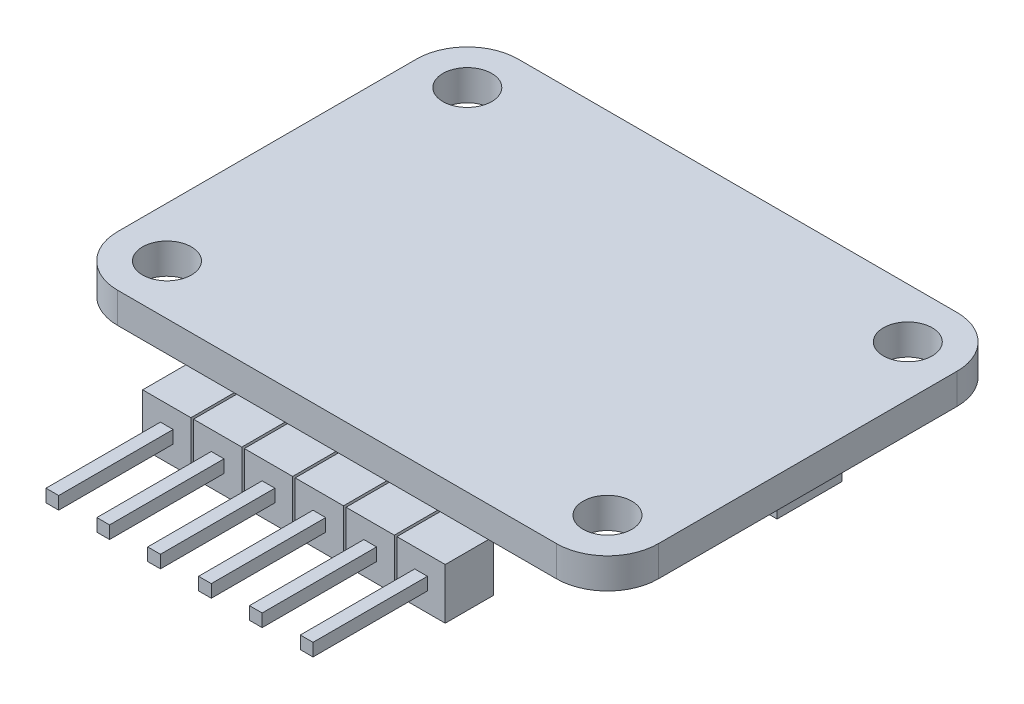
SolidWorks part; units mm, degrees
ref_plane "Front Plane" through (0, 0, 0) normal (0, 0, 1) x (1, 0, 0)
ref_plane "Top Plane" through (0, 0, 0) normal (0, 1, 0) x (1, 0, 0)
ref_plane "Right Plane" through (0, 0, 0) normal (1, 0, 0) x (0, 0, -1)
sketch "Sketch1" plane through (0, 0, 0) normal (0, 1, 0) x (1, 0, 0)
  line L0 (13.5, 20) -> (13.5, 0) construction
  line L1 (0, 20) -> (27, 20)
  line L2 (0, 20) -> (0, 0)
  line L3 (0, 0) -> (27, 0)
  line L4 (27, 20) -> (27, 0)
  line L5 (2.5, 10) -> (24.5, 10) construction
  line L6 (2.5, 17.5) -> (2.5, 2.5) construction
  line L7 (24.5, 17.5) -> (24.5, 2.5) construction
  circle A0 centre (2.5, 17.5) radius 1.2192
  circle A1 centre (24.5, 17.5) radius 1.2192
  circle A2 centre (24.5, 2.5) radius 1.2192
  circle A3 centre (2.5, 2.5) radius 1.2192
  point P13 (13.5, 10)
  dimension "D5" = 2.4384
  dimension "D1" = 27
  dimension "D2" = 20
  dimension "D3" = 22
  dimension "D4" = 15
extrude "Boss-Extrude1" add sketch "Sketch1" along normal blind 1.524
sketch "Sketch2" plane through (0, 1.524, 0) normal (0, 1, 0) x (1, 0, 0)
  line L0 (13.5, 1.524) -> (13.5, 0) construction
  line L1 (7.15, 1.524) -> (9.69, 1.524) construction
  line L2 (9.69, 1.524) -> (12.23, 1.524) construction
  line L3 (12.23, 1.524) -> (14.77, 1.524) construction
  line L4 (14.77, 1.524) -> (17.31, 1.524) construction
  line L5 (17.31, 1.524) -> (19.85, 1.524) construction
  line L6 (0, 0) -> (27, 0) construction
  line L7 (19.85, 1.524) -> (22.39, 1.524) construction
  line L8 (21.12, 12.54) -> (21.12, 7.46) construction
  line L9 (21.12, 10) -> (27, 10) construction
  line L10 (27, 0) -> (27, 20) construction
  line L11 (21.12, 7.46) -> (21.12, 1.524) construction
  point P10 (22.39, 10)
  dimension "D1" = 2.54
  dimension "D2" = 1.524
  dimension "D3" = 5.08
  dimension "D4" = 1.27
sketch "Sketch3" plane through (0, 0, 0) normal (0, -1, 0) x (-1, 0, 0)
  line L0 (-18.6435, -0.9525) -> (-18.5165, -0.9525) construction
  line L21 (-21.0565, 0.254) -> (-18.6435, 0.254)
  line L24 (-13.5635, -0.9525) -> (-13.4365, -0.9525) construction
  line L25 (-15.9765, 0.254) -> (-13.5635, 0.254)
  line L26 (-15.9765, 0.254) -> (-15.9765, -2.159)
  line L27 (-15.9765, -2.159) -> (-13.5635, -2.159)
  line L28 (-13.5635, 0.254) -> (-13.5635, -2.159)
  line L29 (-13.4365, 0.254) -> (-11.0235, 0.254)
  line L30 (-13.4365, 0.254) -> (-13.4365, -2.159)
  line L31 (-13.4365, -2.159) -> (-11.0235, -2.159)
  line L32 (-11.0235, 0.254) -> (-11.0235, -2.159)
  line L33 (-10.8965, 0.254) -> (-8.4835, 0.254)
  line L34 (-10.8965, 0.254) -> (-10.8965, -2.159)
  line L35 (-10.8965, -2.159) -> (-8.4835, -2.159)
  line L36 (-8.4835, 0.254) -> (-8.4835, -2.159)
  line L37 (-8.3565, 0.254) -> (-5.9435, 0.254)
  line L38 (-8.3565, 0.254) -> (-8.3565, -2.159)
  line L39 (-8.3565, -2.159) -> (-5.9435, -2.159)
  line L40 (-5.9435, 0.254) -> (-5.9435, -2.159)
  line L41 (-10.8965, -0.9525) -> (-11.0235, -0.9525) construction
  line L42 (-8.3565, -0.9525) -> (-8.4835, -0.9525) construction
  line L43 (-13.5, 1.524) -> (-13.5, 0) construction
  line L44 (0, 0) -> (-27, 0) construction
  line L45 (-21.0565, 0.254) -> (-21.0565, -2.159)
  line L46 (-21.0565, -2.159) -> (-18.6435, -2.159)
  line L47 (-18.6435, 0.254) -> (-18.6435, -2.159)
  line L48 (-18.5165, 0.254) -> (-16.1035, 0.254)
  line L49 (-18.5165, 0.254) -> (-18.5165, -2.159)
  line L50 (-18.5165, -2.159) -> (-16.1035, -2.159)
  line L51 (-16.1035, 0.254) -> (-16.1035, -2.159)
  line L53 (-15.9765, -0.9525) -> (-16.1035, -0.9525) construction
  point P27 (-13.5, -0.9525)
  dimension "D2" = 0.127
  dimension "D3" = 2.413
  dimension "D5" = 0.254
extrude "Boss-Extrude2" add sketch "Sketch3" along normal blind 2.54
sketch "Sketch4" plane through (0, 0, 2.159) normal (0, 0, 1) x (1, 0, 0)
  line L0 (8.3565, -1.27) -> (5.9435, -1.27) construction
  line L1 (5.9435, -2.54) -> (5.9435, 0) construction
  line L2 (8.3565, -2.54) -> (8.3565, 0) construction
  line L3 (17.6275, -0.9525) -> (16.9925, -0.9525)
  line L4 (17.6275, -0.9525) -> (17.6275, -1.5875)
  line L5 (7.15, -0.9525) -> (7.15, -1.5875) construction
  line L7 (7.4675, -0.9525) -> (7.4675, -1.5875)
  line L8 (7.4675, -0.9525) -> (6.8325, -0.9525)
  line L9 (6.8325, -0.9525) -> (6.8325, -1.5875)
  line L10 (7.4675, -1.5875) -> (6.8325, -1.5875)
  line L134 (10.0075, -0.9525) -> (9.3725, -0.9525)
  line L135 (10.0075, -0.9525) -> (10.0075, -1.5875)
  line L136 (10.0075, -1.5875) -> (9.3725, -1.5875)
  line L137 (9.3725, -0.9525) -> (9.3725, -1.5875)
  line L138 (12.5475, -0.9525) -> (11.9125, -0.9525)
  line L139 (12.5475, -0.9525) -> (12.5475, -1.5875)
  line L140 (12.5475, -1.5875) -> (11.9125, -1.5875)
  line L141 (11.9125, -0.9525) -> (11.9125, -1.5875)
  line L142 (15.0875, -0.9525) -> (14.4525, -0.9525)
  line L143 (15.0875, -0.9525) -> (15.0875, -1.5875)
  line L144 (15.0875, -1.5875) -> (14.4525, -1.5875)
  line L145 (14.4525, -0.9525) -> (14.4525, -1.5875)
  line L146 (17.6275, -1.5875) -> (16.9925, -1.5875)
  line L147 (16.9925, -0.9525) -> (16.9925, -1.5875)
  line L148 (20.1675, -0.9525) -> (19.5325, -0.9525)
  line L149 (20.1675, -0.9525) -> (20.1675, -1.5875)
  line L150 (20.1675, -1.5875) -> (19.5325, -1.5875)
  line L151 (19.5325, -0.9525) -> (19.5325, -1.5875)
  point P8 (7.15, -1.27)
  dimension "D1" = 0.635
  dimension "D2" = 6
extrude "Boss-Extrude3" add sketch "Sketch4" along normal blind 5.715
fillet "Fillet1" radius 2.54 4 edges at (0, 0.762, 0) (27, 0.762, 0) (0, 0.762, -20) (27, 0.762, -20)
sketch "Sketch5" plane through (0, 0, 0) normal (0, -1, 0) x (1, 0, 0)
  line L0 (24.46, -20) -> (2.54, -20) construction
  line L1 (17.3948, -13.5425) -> (25.1799, -13.5425)
  line L2 (17.3948, -13.5425) -> (17.3948, -10.2913)
  line L3 (17.3948, -10.2913) -> (25.1799, -10.2913)
  line L4 (25.1799, -13.5425) -> (25.1799, -10.2913)
  line L5 (27, -2.54) -> (27, -17.46) construction
  line L6 (23.5078, -11.9169) -> (25.1799, -11.9169) construction
  circle A0 centre (23.5078, -11.9169) radius 0.381
  dimension "D3" = 0.762
  dimension "D1" = 7.7851
  dimension "D2" = 3.2512
extrude "Boss-Extrude4" add sketch "Sketch5" along normal blind 2.1971
